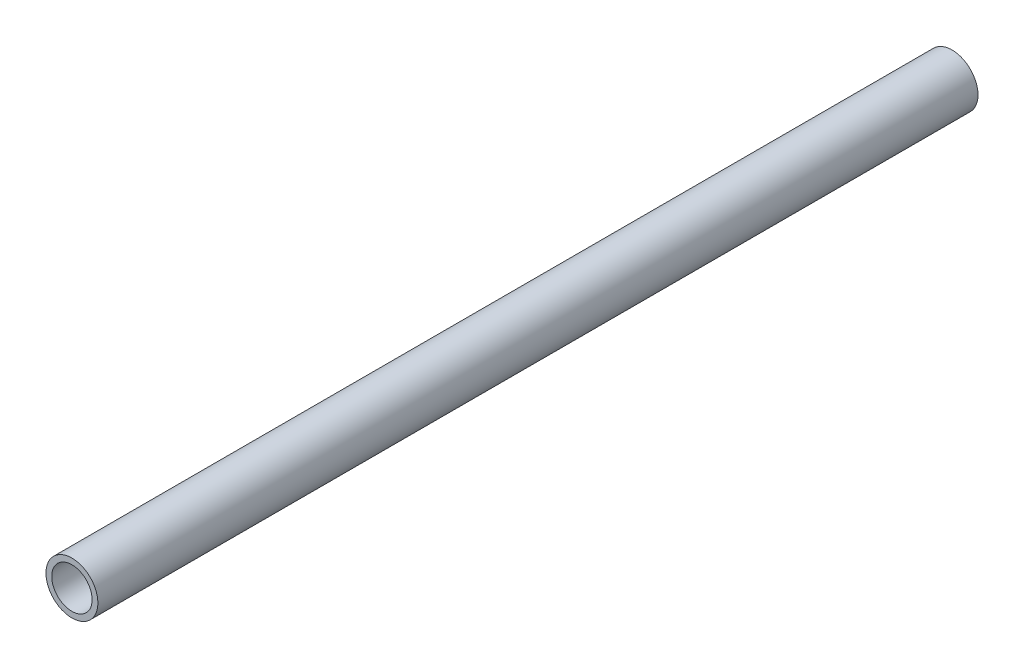
SolidWorks part; units mm, degrees
ref_plane "Face" through (0, 0, 0) normal (0, 0, 1) x (1, 0, 0)
ref_plane "Dessus" through (0, 0, 0) normal (0, 1, 0) x (1, 0, 0)
ref_plane "Droite" through (0, 0, 0) normal (1, 0, 0) x (0, 0, -1)
sketch "Esquisse1" plane through (0, 0, 0) normal (0, 0, 1) x (1, 0, 0)
  circle A0 centre (0, 0) radius 9
  dimension "D1" = 18
extrude "Extrusion1" add sketch "Esquisse1" along normal blind 305
hole_wizard "Trou taraudé M16x2.01" positions "Esquisse5" profile "Esquisse6" tap size "M16x2.0" standard "ISO"
sketch "Esquisse5" plane through (0, 0, 305) normal (0, 0, 1) x (1, 0, 0)
  circle A0 centre (0, 0) radius 9 construction
  point P0 (0, 0)
sketch "Esquisse6" plane through (0, 0, 305) normal (1, 0, 0) x (0, -1, 0)
  line L0 (0, 0) -> (0, 305)
  line L1 (0, 305) -> (7, 305)
  line L2 (7, 305) -> (7, 0)
  line L5 (7, 0) -> (0, 0)
  line L11 (0, -6.35) -> (0, 107.95) construction
  dimension "Diamètre du trou pour taraudage jusqu'au prochain" = 14
  dimension "Profondeur du trou pour taraudage jusqu'au prochain" = 305
cosmetic thread "Représentation de filetage1" parameters "D1"=32, "D2"=16
